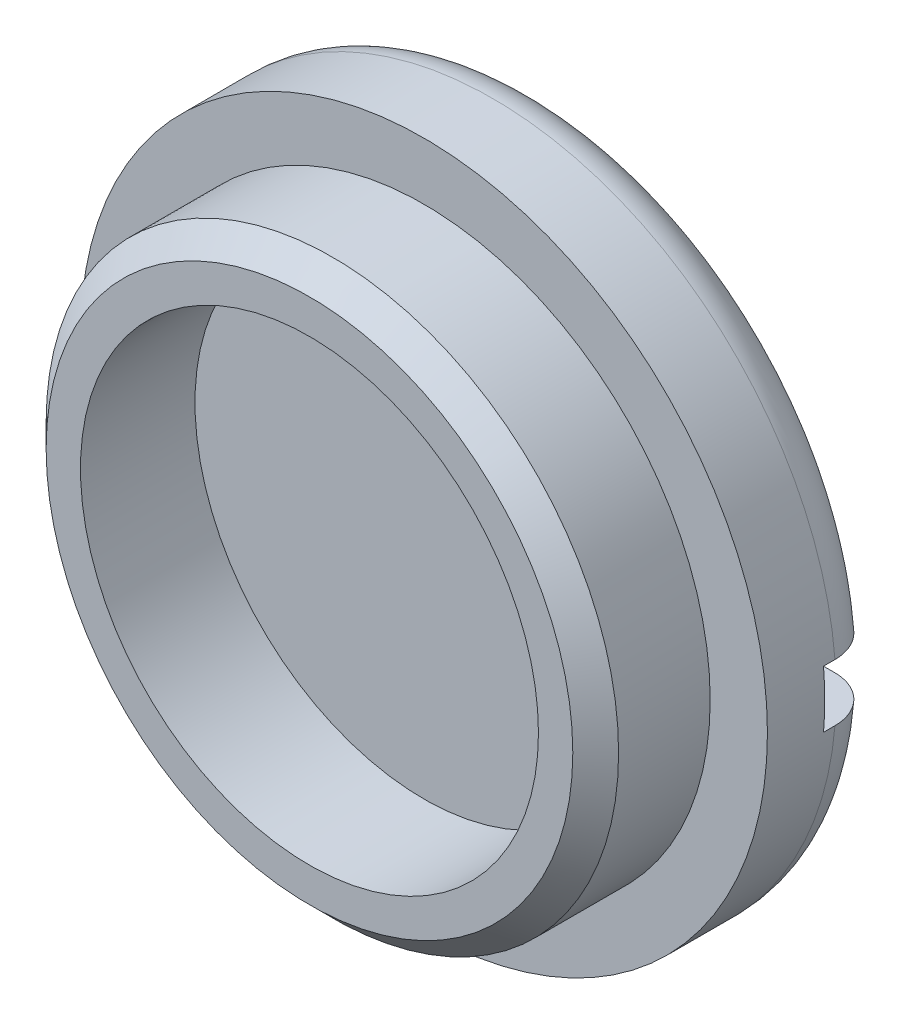
SolidWorks part; units mm, degrees
material "6061 Alloy"
ref_plane "Front Plane" through (0, 0, 0) normal (0, 0, 1) x (1, 0, 0)
ref_plane "Top Plane" through (0, 0, 0) normal (0, 1, 0) x (1, 0, 0)
ref_plane "Right Plane" through (0, 0, 0) normal (1, 0, 0) x (0, 0, -1)
sketch "Sketch1" plane through (0, 0, 0) normal (0, 1, 0) x (1, 0, 0)
  line L0 (-71.1913, 0) -> (106.3165, 0) construction
  line L1 (0, -31.989) -> (0, 60.2146) construction
  line L2 (12.7, 0) -> (15.875, 0)
  line L3 (15.875, 0) -> (15.875, 6.35)
  line L4 (15.875, 6.35) -> (19.05, 6.35)
  line L5 (19.05, 6.35) -> (19.05, 12.7)
  line L6 (19.05, 12.7) -> (0, 12.7)
  line L7 (0, 12.7) -> (0, 6.35)
  line L8 (0, 6.35) -> (12.7, 6.35)
  line L9 (12.7, 6.35) -> (12.7, 0)
  dimension "D1" = 3.175
  dimension "D2" = 15.875
  dimension "D3" = 6.35
  dimension "D4" = 19.05
  dimension "D5" = 12.7
revolve "Revolve1" add sketch "Sketch1" angle 360 about L1
sketch "Sketch2" plane through (0, 0, 0) normal (1, 0, 0) x (0, 0, -1)
  line L0 (0, 0) -> (22.1539, 0) construction
  line L1 (12.7, -19.05) -> (12.7, 19.05) construction
  line L2 (12.7, -19.05) -> (12.7, 19.05) construction
  line L3 (12.7, -1.5875) -> (9.525, -1.5875)
  line L4 (9.525, -1.5875) -> (9.525, 1.5875)
  line L5 (12.7, 1.5875) -> (9.525, 1.5875)
  point P9 (9.525, 0)
  dimension "D1" = 1.5875
  dimension "D2" = 3.175
extrude "Cut-Extrude1" cut sketch "Sketch2" against normal through all and the other way through all
fillet "Fillet1" radius 2.54 2 edges at (0, 19.05, -12.7) (0, -19.05, -12.7)
chamfer "Chamfer1" distance 1.27 angle 45 1 edges at (15.875, 0, 0)
